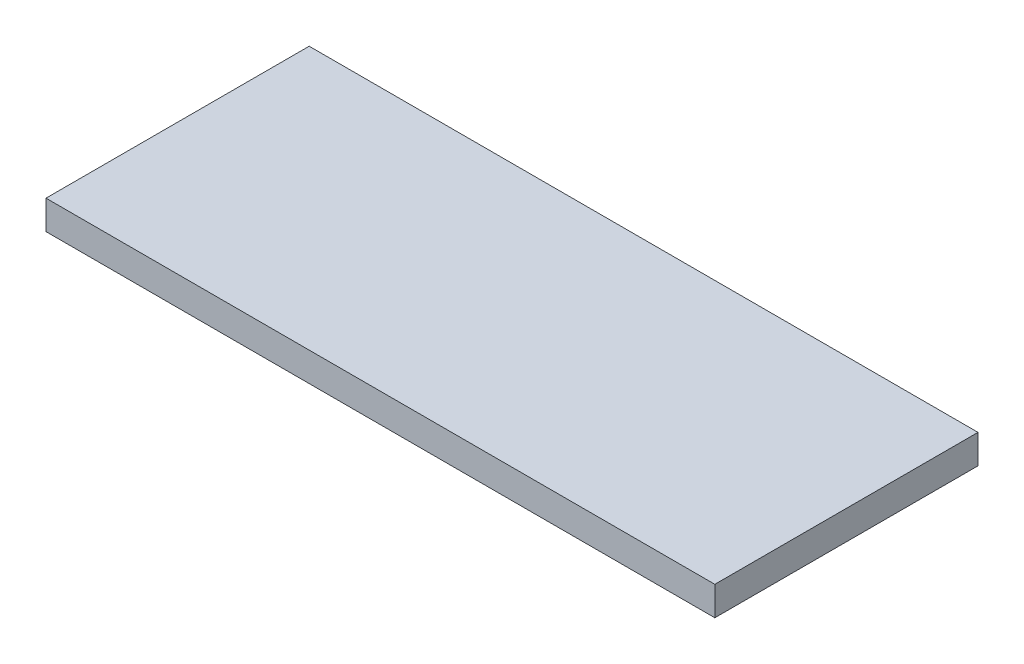
SolidWorks part; units mm, degrees
ref_plane "Front Plane" through (0, 0, 0) normal (0, 0, 1) x (1, 0, 0)
ref_plane "Top Plane" through (0, 0, 0) normal (0, 1, 0) x (1, 0, 0)
ref_plane "Right Plane" through (0, 0, 0) normal (1, 0, 0) x (0, 0, -1)
sketch "Sketch1" plane through (0, 0, 0) normal (0, 1, 0) x (1, 0, 0)
  line L1 (0, 0) -> (415, 0)
  line L2 (0, 0) -> (0, 163.3)
  line L3 (0, 163.3) -> (415, 163.3)
  line L4 (415, 0) -> (415, 163.3)
extrude "Boss-Extrude1" add sketch "Sketch1" along normal blind 18
